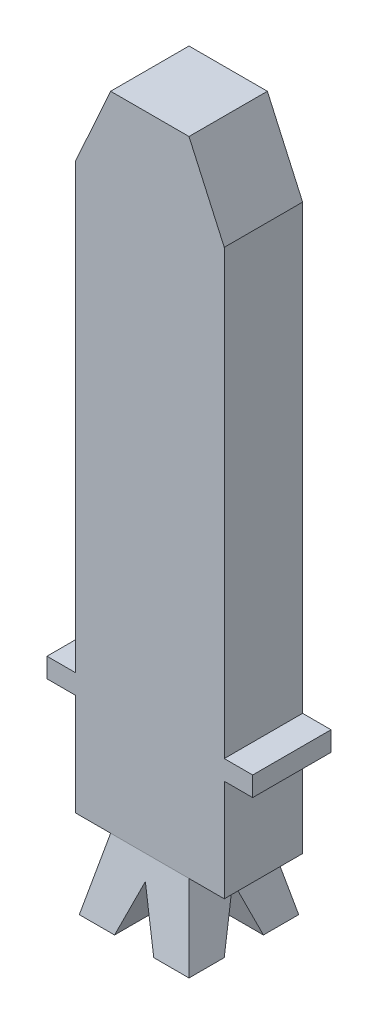
SolidWorks part; units mm, degrees
ref_plane "Front Plane" through (0, 0, 0) normal (0, 0, 1) x (1, 0, 0)
ref_plane "Top Plane" through (0, 0, 0) normal (0, 1, 0) x (1, 0, 0)
ref_plane "Right Plane" through (0, 0, 0) normal (1, 0, 0) x (0, 0, -1)
sketch "Sketch1" plane through (0, 0, 0) normal (0, 0, 1) x (1, 0, 0)
  line L0 (1.9, 0) -> (2.625, 0)
  line L2 (-1.9, 11.3) -> (-1.9, 0)
  line L4 (1.9, 11.3) -> (1.9, 0)
  line L5 (-2.625, 0) -> (-1.9, 0)
  line L6 (-2.625, 0) -> (-2.625, -0.5)
  line L7 (-2.625, -0.5) -> (-1.9, -0.5)
  line L8 (2.625, 0) -> (2.625, -0.5)
  line L9 (1.9, -0.5) -> (2.625, -0.5)
  line L11 (-1.9, -0.5) -> (-1.9, -3.1)
  line L12 (-1.9, -3.1) -> (1.9, -3.1)
  line L13 (1.9, -0.5) -> (1.9, -3.1)
  line L14 (-1, 13.3) -> (1, 13.3)
  line L15 (-1.9, 11.3) -> (-1, 13.3)
  line L16 (1, 13.3) -> (1.9, 11.3)
  point P9 (2.625, -0.25)
  dimension "D2" = 3.8
  dimension "D3" = 1.9
  dimension "D5" = 5.25
  dimension "D6" = 2.625
  dimension "D1" = 2.6
  dimension "D7" = 1.9
  dimension "D8" = 1.9
  dimension "D9" = 0.25
  dimension "D10" = 0.5
  dimension "D11" = 2
  dimension "D13" = 0.9
  dimension "D14" = 3.8
  dimension "D4" = 11.3
  dimension "D12" = 13.3
extrude "Boss-Extrude1" add sketch "Sketch1" along normal blind 2
ref_plane "Plane1" through (0, -4.9, 0) normal (0, -1, 0) x (-1, 0, 0)
sketch "Sketch2" plane through (0, -3.1, 0) normal (0, -1, 0) x (1, 0, 0)
  line L0 (-1.9, 2) -> (1.9, 2) construction
  line L1 (-1, 2) -> (1, 2)
  line L2 (-1, 2) -> (-1, 0)
  line L3 (-1, 0) -> (1, 0)
  line L4 (1, 2) -> (1, 0)
  line L5 (-1.9, 0) -> (1.9, 0) construction
  dimension "D1" = 2
  dimension "D2" = 2
  dimension "D3" = 1
sketch "Sketch3" plane through (0, -4.9, 0) normal (0, -1, 0) x (-1, 0, 0)
  line L1 (-1.4, 0.4) -> (1.4, 0.4)
  line L2 (-1.4, 0.4) -> (-1.4, -2.4)
  line L3 (-1.4, -2.4) -> (1.4, -2.4)
  line L4 (1.4, 0.4) -> (1.4, -2.4)
  dimension "D1" = 2.8
  dimension "D2" = 2.8
  dimension "D3" = 1.4
  dimension "D4" = 0.4
loft "Loft1" add profiles "Sketch2", "Sketch3"
ref_plane "Plane2" through (0, 0, 1.8) normal (0, 0, 1) x (1, 0, 0)
sketch "Sketch4" plane through (0, 0, 1.8) normal (0, 0, 1) x (1, 0, 0)
  line L0 (0, -3.6115) -> (-0.5, -4.9)
  line L1 (-1.1, -4.9) -> (1.1, -4.9) construction
  line L2 (-0.5, -4.9) -> (0.5, -4.9)
  line L3 (0.5, -4.9) -> (0, -3.6115)
  dimension "D1" = 0.5
  dimension "D2" = 0.5
  dimension "D3" = 3.6115
ref_plane "Plane3" through (1.8, 0, 0) normal (1, 0, 0) x (0, 0, -1)
sketch "Sketch5" plane through (1.8, 0, -1.8) normal (-1, 0, 0) x (0, 0, 1)
  line L0 (2.8, -3.6115) -> (2.3, -4.9)
  line L1 (1.4, -4.9) -> (4.2, -4.9) construction
  line L2 (2.3, -4.9) -> (3.3, -4.9)
  line L3 (3.3, -4.9) -> (2.8, -3.6115)
  line L4 (1.4, -4.9) -> (4.2, -4.9) construction
extrude "Cut-Extrude1" cut sketch "Sketch4" against normal through all both and the other way through all
extrude "Cut-Extrude2" cut sketch "Sketch5" against normal through all both and the other way through all
equation "\"D3@Sketch1\"=\"D2@Sketch1\"/2"
equation "\"D6@Sketch1\"=\"D5@Sketch1\"/2"
equation "\"D3@Sketch3\"=\"D1@Sketch3\"/2"
equation "\"D4@Sketch3\"=(\"D2@Sketch3\"-2)/2"
